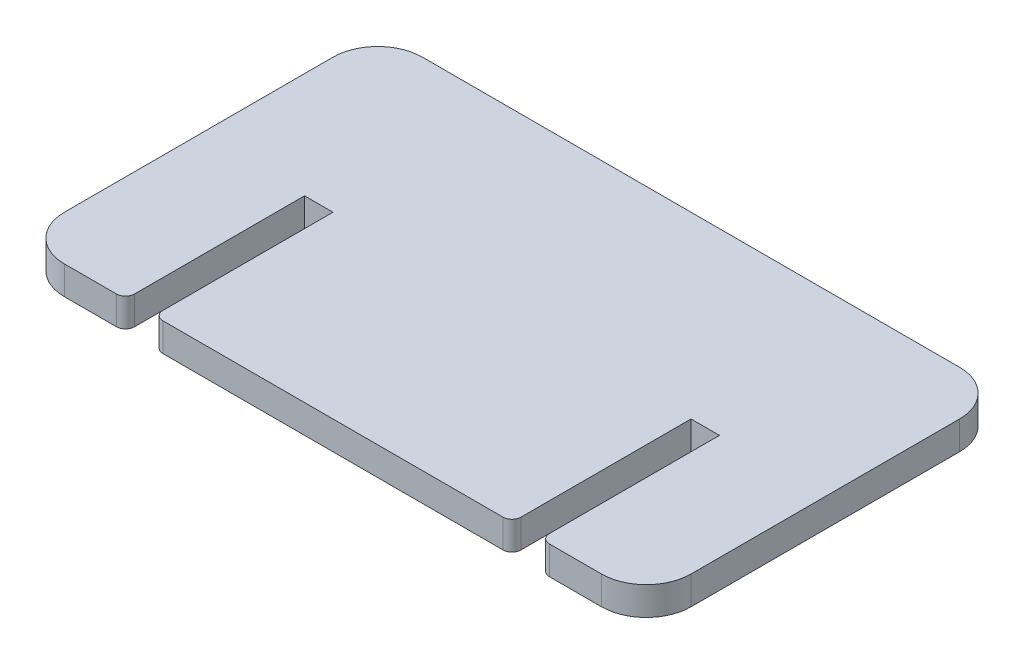
SolidWorks part; units mm, degrees
ref_plane "Front Plane" through (0, 0, 0) normal (0, 0, 1) x (1, 0, 0)
ref_plane "Top Plane" through (0, 0, 0) normal (0, 1, 0) x (1, 0, 0)
ref_plane "Right Plane" through (0, 0, 0) normal (1, 0, 0) x (0, 0, -1)
sketch "Sketch1" plane through (0, 0, 0) normal (0, 1, 0) x (1, 0, 0)
  line L1 (5, 0) -> (65, 0)
  line L2 (0, 5) -> (0, 35)
  line L3 (5, 40) -> (65, 40)
  line L4 (70, 5) -> (70, 35)
  arc A0 (70, 5) -> (65, 0) centre (65, 5) cw
  arc A1 (70, 35) -> (65, 40) centre (65, 35) ccw
  arc A2 (5, 40) -> (0, 35) centre (5, 35) ccw
  arc A3 (0, 5) -> (5, 0) centre (5, 5) ccw
  point P7 (70, 0)
  point P12 (0, 40)
  point P15 (0, 0)
  dimension "D3" = 5
  dimension "D1" = 70
  dimension "D2" = 40
extrude "Boss-Extrude1" add sketch "Sketch1" along normal blind 3.175
sketch "Sketch2" plane through (0, 3.175, 0) normal (0, 1, 0) x (1, 0, 0)
  line L0 (5, 0) -> (65, 0) construction
  line L1 (11.825, 0) -> (15, 0)
  line L2 (11.825, 0) -> (11.825, 20)
  line L3 (11.825, 20) -> (15, 20)
  line L4 (15, 0) -> (15, 20)
  line L5 (0, 35) -> (0, 5) construction
  line L6 (58.175, 0) -> (55, 0)
  line L7 (58.175, 0) -> (58.175, 20)
  line L8 (58.175, 20) -> (55, 20)
  line L9 (55, 0) -> (55, 20)
  point P12 (0, 20)
  point P13 (35, 0)
  dimension "D1" = 3.175
  dimension "D2" = 3.175
  dimension "D3" = 40
  dimension "D4" = 20
extrude "Cut-Extrude1" cut sketch "Sketch2" against normal through all
fillet "Fillet1" radius 1 4 edges at (58.175, 1.5875, 0) (55, 1.5875, 0) (15, 1.5875, 0) (11.825, 1.5875, 0)
